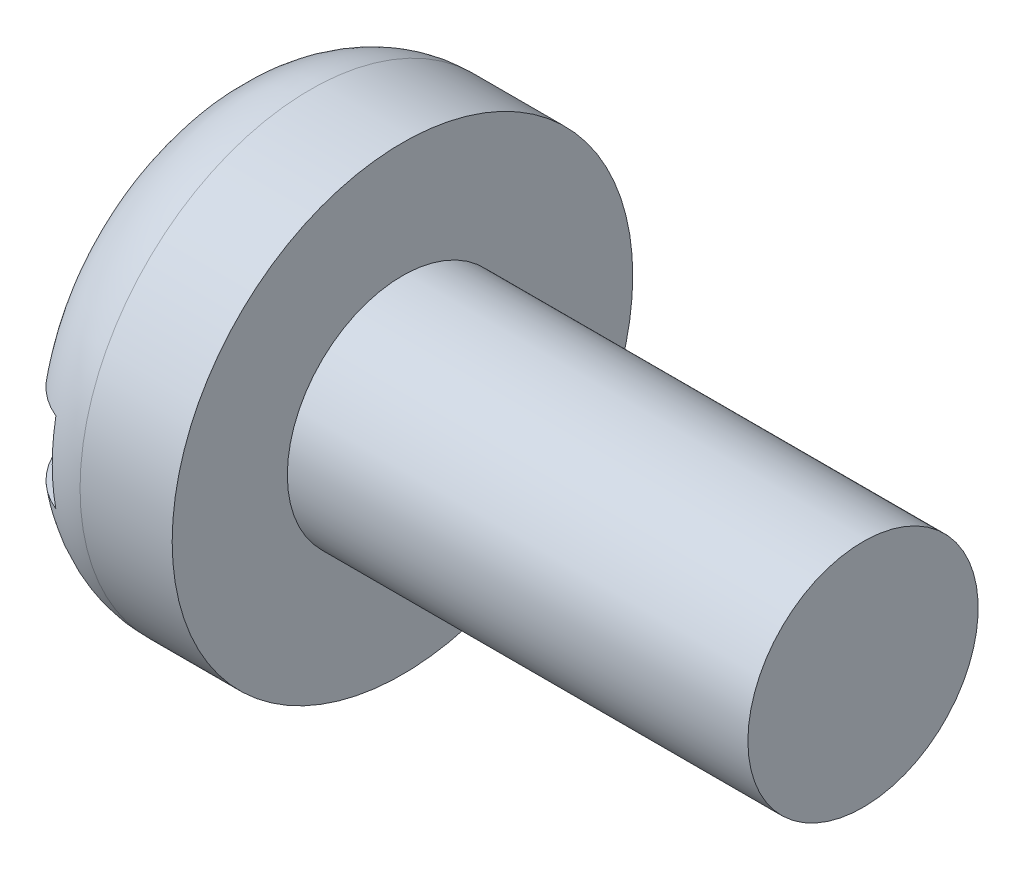
SolidWorks part; units mm, degrees
ref_plane "Plane1" through (0, 0, 0) normal (0, 0, 1) x (1, 0, 0)
ref_plane "Plane2" through (0, 0, 0) normal (0, 1, 0) x (1, 0, 0)
ref_plane "Plane3" through (0, 0, 0) normal (1, 0, 0) x (0, 0, -1)
revolve "Base-Revolve" add sketch "BodySke" angle 360 about L2
sketch "BodySke" plane through (0, 0, 0) normal (0, 0, 1) x (1, 0, 0)
  line L0 (1.6, 1) -> (1.6, 2)
  line L1 (0, 0) -> (0, 1.2)
  line L2 (-25.4, 0) -> (127, 0) construction
  line L3 (5.6, 0) -> (0, 0)
  line L4 (1.6, 1) -> (5.6, 1)
  line L5 (5.6, 1) -> (5.6, 0)
  line L6 (0.8, 2) -> (1.6, 2)
  line L7 (1.6, -1) -> (5.6, -1) construction
  line L8 (0, -2) -> (1.6, -2) construction
  line L9 (2, 2.5875) -> (2, -6.9375) construction
  line L10 (1.6, 6.35) -> (1.6, -3.175) construction
  arc A0 (0, 1.2) -> (0.8, 2) centre (0.8, 1.2) cw
  point P15 (0, 2)
  dimension "Head_fillet_rad" = 0.8
  dimension "Head_ht" = 1.6
  dimension "Diameter" = 2
  dimension "Length" = 4
  dimension "Head_dia" = 4
  dimension "Advance" = 0.4
  dimension "Thread_nom" = 4
cosmetic thread "ThreadCosmetic" [suppressed] parameters "Thread_length"=3.6, "Thread_minor"=1.548
sketch "Sketch2" plane through (0, 0, 0) normal (1, 0, 0) x (0, 0, -1)
  line L0 (2, -0.35) -> (-2, -0.35)
  line L1 (2, -0.35) -> (2, 0.35)
  line L2 (-2, 0.35) -> (2, 0.35)
  line L3 (-2, 0.35) -> (-2, -0.35)
  dimension "D1" = 4
  dimension "D2" = 2
  dimension "Slot_width" = 0.7
  dimension "D3" = 0.35
extrude "Slot" cut sketch "Sketch2" along normal blind 0.5
sketch "ThdSchSke" plane through (0, 0, 0) normal (0, 0, 1) x (1, 0, 0)
  line L0 (2, -0.774) -> (1.8418, -1)
  line L1 (2, -0.774) -> (2.1582, -1)
  line L2 (2.1582, -1) -> (2.1582, -1.25)
  line L3 (-3.175, 0) -> (5.1513, 0) construction
  line L5 (2.1582, -1.25) -> (1.8418, -1.25)
  line L6 (1.8418, -1.25) -> (1.8418, -1)
  dimension "Thread_minor" = 1.548
  dimension "Diameter" = 2
  dimension "Start" = 2
  dimension "SideAngle" = 55
  dimension "VeeAngle" = 70
  dimension "Overcut" = 2.5
revolve "ThreadSchematic" [suppressed] cut sketch "ThdSchSke" angle 360 about L3
pattern_linear "ThdSchPat" [suppressed]
equation "\"D1@Sketch2\" = \"Head_dia@BodySke\""
equation "\"D2@Sketch2\" = \"D1@Sketch2\" / 2"
equation "\"D3@Sketch2\" = \"Slot_width@Sketch2\" / 2"
equation "\"Thread_length@ThreadCosmetic\" = ((sgn( (\"Length@BodySke\" - \"Advance@BodySke\" ) - \"Thread_nom@BodySke\" )-1)*( (\"Length@BodySke\" - \"Advance@BodySke\" ) - \"Thread_nom@BodySke\" ))/-2+ \"Thread_nom@BodySke\""
equation "\"Thread_minor@ThdSchSke\" = \"Thread_minor@ThreadCosmetic\""
equation "\"Diameter@ThdSchSke\" = \"Diameter@BodySke\""
equation "\"Overcut@ThdSchSke\" = \"Diameter@BodySke\" * 1.25"
equation "\"Start@ThdSchSke\" = \"Head_ht@BodySke\" + \"Length@BodySke\" - \"Thread_length@ThreadCosmetic\"  '---Non-countersunk---"
equation "\"Num_threads@ThdSchPat\" = int( \"Thread_length@ThreadCosmetic\" / \"Advance@BodySke\" + 0.999 )  + 1"
equation "\"Advance@ThdSchPat\" = \"Thread_length@ThreadCosmetic\" /  (\"Num_threads@ThdSchPat\" - 1) 'relax it"
